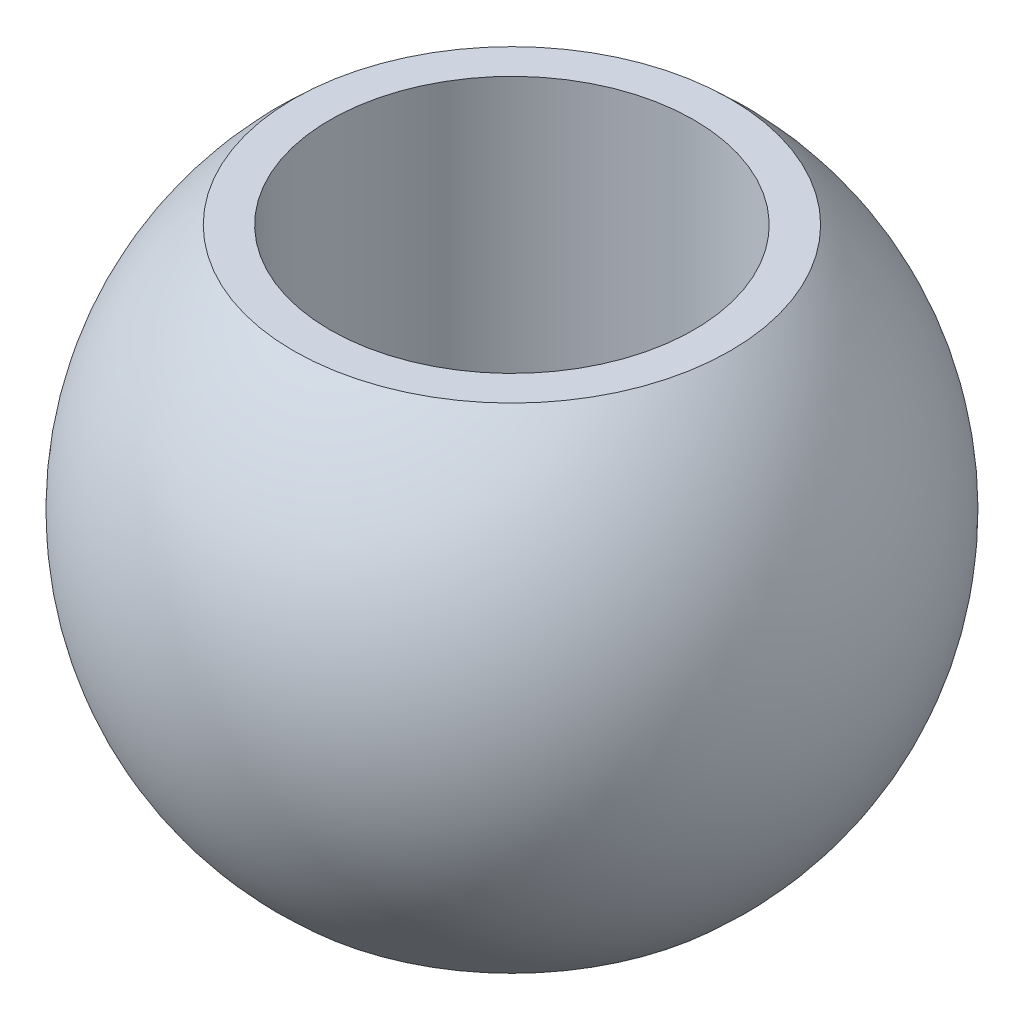
SolidWorks part; units mm, degrees
material "1.0545 (S355N)"
ref_plane "Płaszczyzna przednia" through (0, 0, 0) normal (0, 0, 1) x (1, 0, 0)
ref_plane "Płaszczyzna górna" through (0, 0, 0) normal (0, 1, 0) x (1, 0, 0)
ref_plane "Płaszczyzna prawa" through (0, 0, 0) normal (1, 0, 0) x (0, 0, -1)
sketch "Szkic1" plane through (0, 0, 0) normal (0, 0, 1) x (1, 0, 0)
  line L0 (0, -11.1) -> (0, 11.1) construction
  line L1 (7, -9.5) -> (7, 9.5)
  line L2 (7, 9.5) -> (8.3984, 9.5)
  line L3 (7, -9.5) -> (8.3984, -9.5)
  arc A0 (8.3984, -9.5) -> (8.3984, 9.5) centre (0, 0) ccw
  point P6 (7, 0)
  dimension "d3" = 25.36
  dimension "d1" = 7
  dimension "b1" = 19
revolve "Obrót1" add sketch "Szkic1" angle 360 about L0
